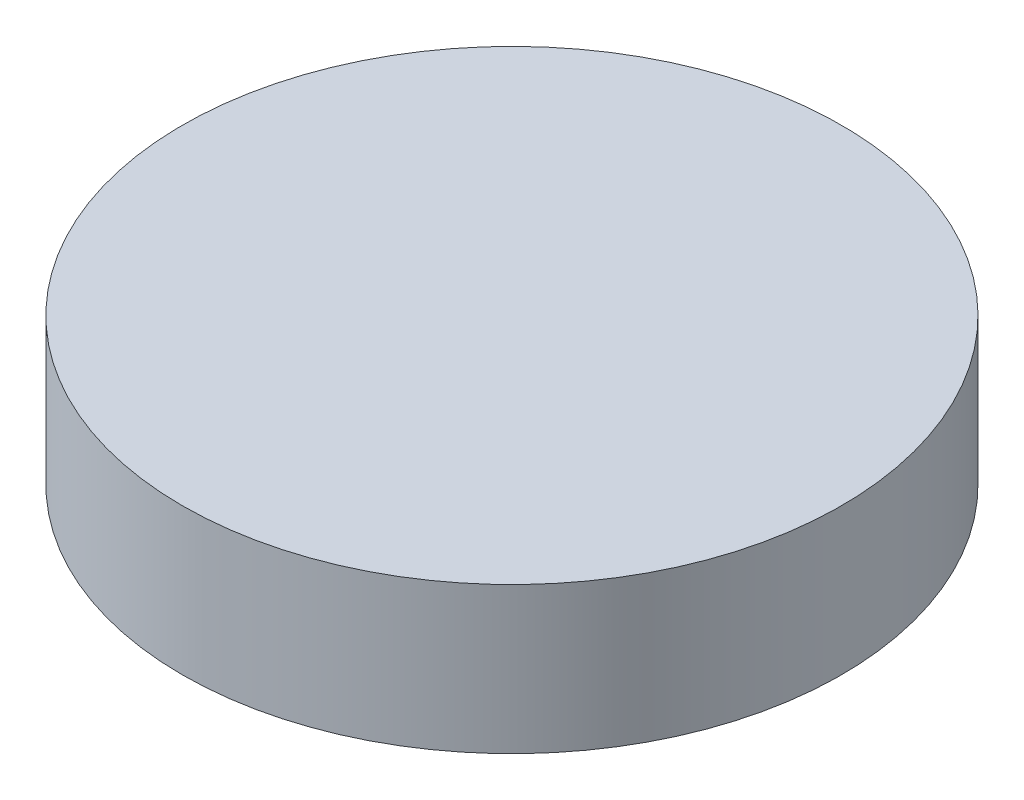
SolidWorks part; units mm, degrees
ref_plane "Front Plane" through (0, 0, 0) normal (0, 0, 1) x (1, 0, 0)
ref_plane "Top Plane" through (0, 0, 0) normal (0, 1, 0) x (1, 0, 0)
ref_plane "Right Plane" through (0, 0, 0) normal (1, 0, 0) x (0, 0, -1)
sketch "Sketch1" plane through (0, 0, 0) normal (0, 1, 0) x (1, 0, 0)
  circle A0 centre (0, 0) radius 114.3
  dimension "D1" = 228.6
extrude "Boss-Extrude1" add sketch "Sketch1" along normal blind 50.8
